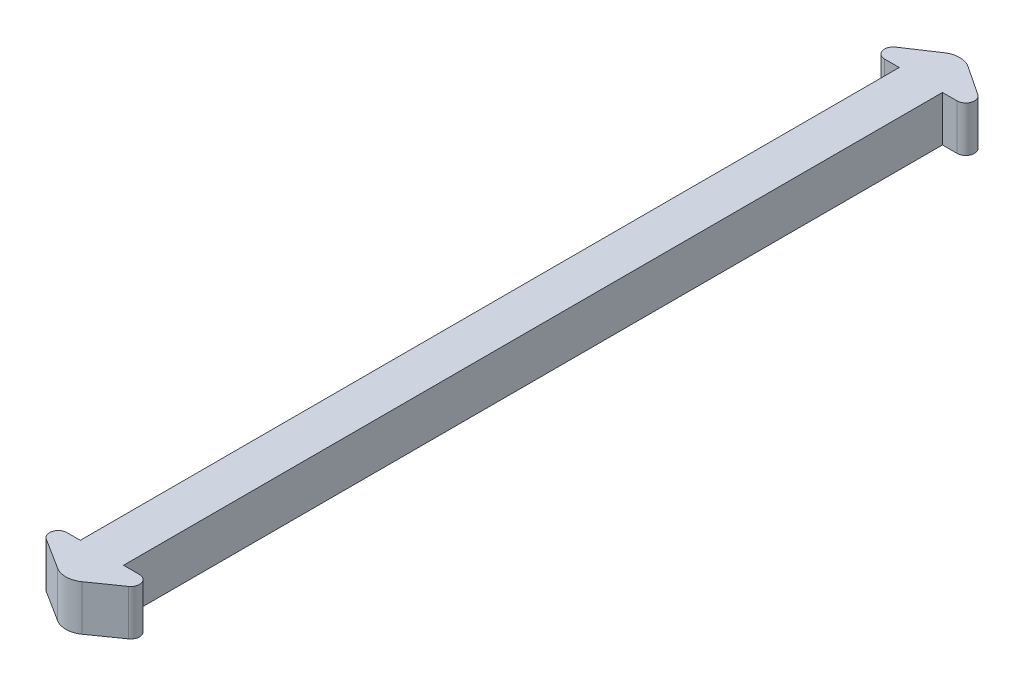
SolidWorks part; units mm, degrees
ref_plane "Front Plane" through (0, 0, 0) normal (0, 0, 1) x (1, 0, 0)
ref_plane "Top Plane" through (0, 0, 0) normal (0, 1, 0) x (1, 0, 0)
ref_plane "Right Plane" through (0, 0, 0) normal (1, 0, 0) x (0, 0, -1)
sketch "Sketch1" plane through (0, 0, 0) normal (0, 1, 0) x (1, 0, 0)
  line L0 (-2.0275, 5.4092) -> (-2.0275, 14.9092)
  line L1 (-6.7775, 5.4092) -> (2.7225, 5.4092)
  line L2 (-6.7775, 5.4092) -> (-6.7775, -174.5908)
  line L4 (2.7225, 5.4092) -> (2.7225, -174.5908)
  line L5 (2.7225, 5.4092) -> (12.2225, 5.4092)
  line L6 (-16.2775, 5.4092) -> (-6.7775, 5.4092)
  line L7 (-16.2775, 5.4092) -> (-2.0275, 14.9092)
  line L8 (12.2225, 5.4092) -> (-2.0275, 14.9092)
  line L9 (12.2225, -174.5908) -> (-1.2775, -184.0908)
  line L10 (-16.2775, -174.5908) -> (-1.2775, -184.0908)
  line L11 (-16.2775, -174.5908) -> (-6.7775, -174.5908)
  line L12 (2.7225, -174.5908) -> (12.2225, -174.5908)
  line L13 (-6.7775, -174.5908) -> (2.7225, -174.5908)
  dimension "D1" = 9.5
  dimension "D2" = 180
  dimension "D3" = 9.5
  dimension "D4" = 9.5
  dimension "D5" = 9.5
  dimension "D6" = 9.5
  dimension "D7" = 9.5
  dimension "D8" = 9.5
extrude "Boss-Extrude1" add sketch "Sketch1" along normal blind 10 contours L2 L13 L4 L1 | L7 L6 L1 L0 | L5 L8 L0 L1 | L13 L11 L10 L9 L12
fillet "Fillet1" radius 1.9 4 edges at (12.2225, 5, -5.4092) (12.2225, 5, 174.5908) (-16.2775, 5, 174.5908) (-16.2775, 5, -5.4092)
fillet "Fillet2" radius 4.75 2 edges at (-1.2775, 5, 184.0908) (-2.0275, 5, -14.9092)
